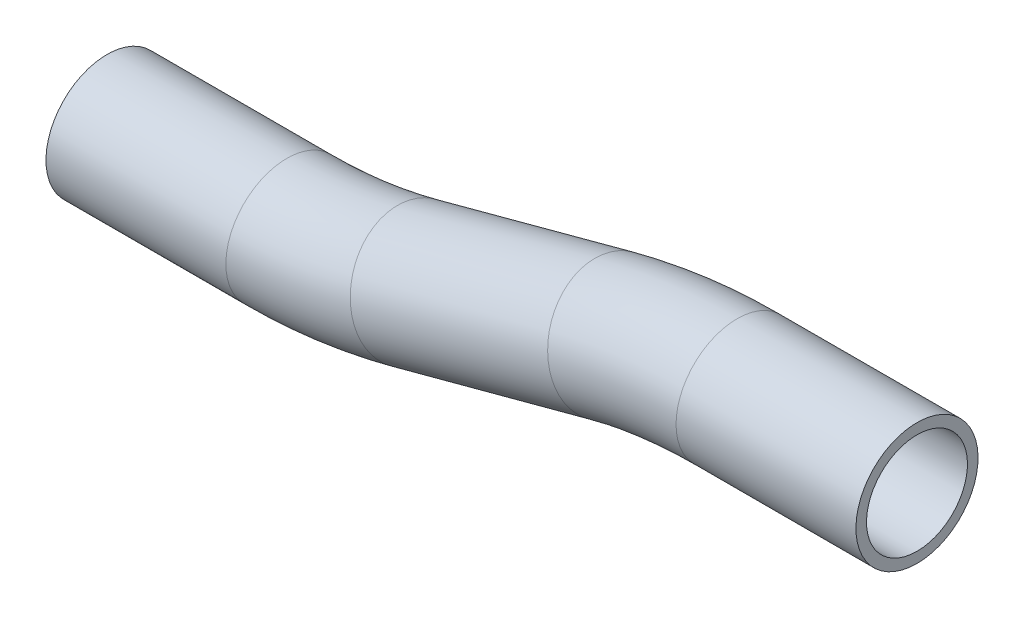
SolidWorks part; units mm, degrees
material "6061 Alloy"
ref_plane "Front Plane" through (0, 0, 0) normal (0, 0, 1) x (1, 0, 0)
ref_plane "Top Plane" through (0, 0, 0) normal (0, 1, 0) x (1, 0, 0)
ref_plane "Right Plane" through (0, 0, 0) normal (1, 0, 0) x (0, 0, -1)
sketch "Sketch1" plane through (0, 0, 0) normal (0, 0, 1) x (1, 0, 0)
  line L0 (0, 0) -> (28.0681, 0)
  line L2 (-19.722, -2.5965) -> (-50.524, -10.8498)
  line L3 (-50.524, -10.8498) -> (-10.0319, 0)
  line L4 (28.0681, 0) -> (-10.0319, 0)
  line L5 (-70.246, -13.4463) -> (-98.3141, -13.4463)
  line L6 (-98.3141, -13.4463) -> (-60.2141, -13.4463)
  line L7 (-19.722, -2.5965) -> (-60.2141, -13.4463)
  arc A0 (0, 0) -> (-19.722, -2.5965) centre (0, -76.2) ccw
  arc A1 (-50.524, -10.8498) -> (-70.246, -13.4463) centre (-70.246, 62.7537) cw
  point P9 (-10.0319, 0)
  point P14 (-60.2141, -13.4463)
  dimension "D3" = 15
  dimension "D4" = 15
  dimension "D1" = 76.2
  dimension "D2" = 76.2
  dimension "D5" = 51.9524
  dimension "D6" = 38.1
  dimension "D7" = 38.1
ref_plane "Plane1" through (28.0681, 0, 0) normal (-1, 0, 0) x (0, 0, 1)
sketch "Sketch2" plane through (28.0681, 0, 0) normal (-1, 0, 0) x (0, 0, 1)
  circle A0 centre (0, 0) radius 9.525
  circle A1 centre (0, 0) radius 7.874
  dimension "D1" = 19.05
  dimension "D2" = 15.748
sweep "Sweep1" add profiles "Sketch2" path "Sketch1"
sketch "Sketch4" plane through (-98.3141, 0, 0) normal (-1, 0, 0) x (0, 0, 1)
  line L0 (-7.874, -13.4463) -> (7.874, -13.4463) construction
